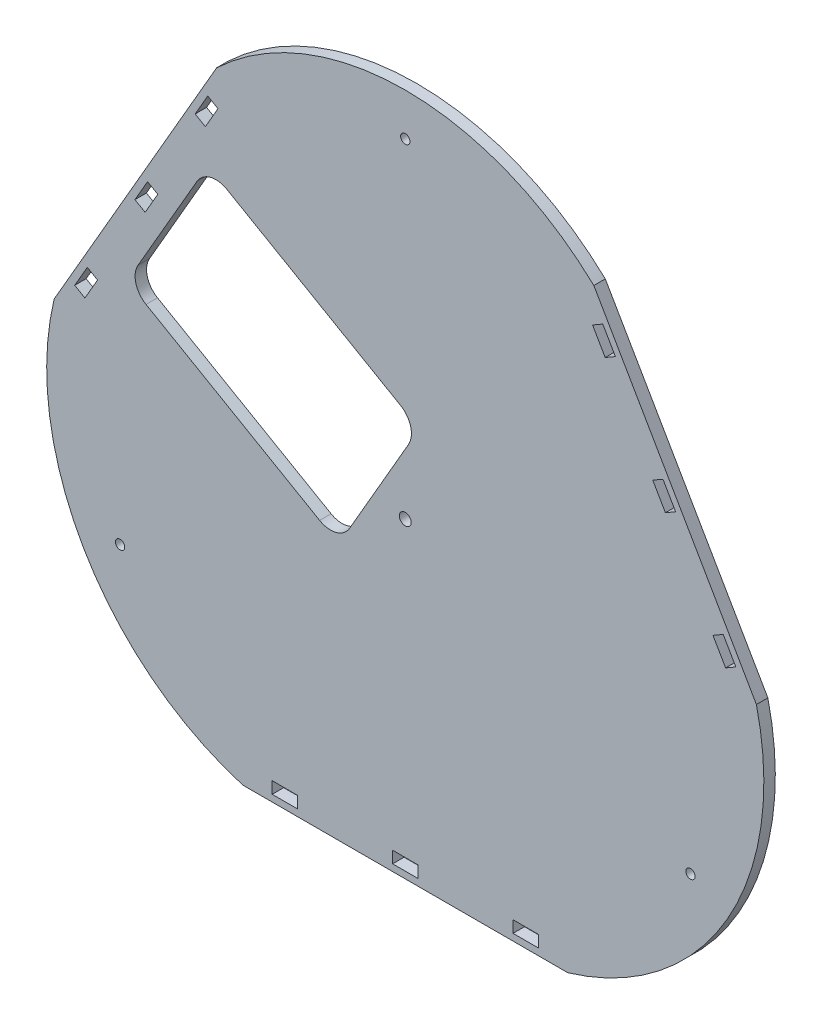
SolidWorks part; units mm, degrees
ref_plane "Front Plane" through (0, 0, 0) normal (0, 0, 1) x (1, 0, 0)
ref_plane "Top Plane" through (0, 0, 0) normal (0, 1, 0) x (1, 0, 0)
ref_plane "Right Plane" through (0, 0, 0) normal (1, 0, 0) x (0, 0, -1)
sketch "Sketch1" plane through (0, 0, 0) normal (0, 0, 1) x (1, 0, 0)
  line L0 (-96.5063, -185) -> (96.5063, -185)
  line L1 (208.4678, 8.9231) -> (111.9616, 176.0769)
  line L2 (-111.9616, 176.0769) -> (-208.4678, 8.9231)
  line L3 (0, 0) -> (-160.2147, 92.5) construction
  line L4 (0, 0) -> (160.2147, 92.5) construction
  line L5 (0, 0) -> (0, -185) construction
  arc A0 (-208.4678, 8.9231) -> (-96.5063, -185) centre (-49.8946, -28.8067) ccw
  arc A1 (96.5063, -185) -> (208.4678, 8.9231) centre (49.8946, -28.8067) ccw
  arc A2 (111.9616, 176.0769) -> (-111.9616, 176.0769) centre (0, 57.6133) ccw
  circle A3 centre (0, 0) radius 3.5
  dimension "D1" = 163
  dimension "D6" = 7
  dimension "D2" = 193.0125
  dimension "D3" = 60
  dimension "D4" = 185
  dimension "D5" = 120
extrude "Boss-Extrude1" add sketch "Sketch1" along normal blind 6.8
sketch "Sketch2" plane through (0, 0, 6.8) normal (0, 0, 1) x (1, 0, 0)
  line L4 (7.5, -174) -> (-7.5, -174)
  line L8 (7.5, -181) -> (7.5, -174)
  line L9 (-7.5, -174) -> (-7.5, -181)
  line L10 (-7.5, -181) -> (7.5, -181)
  line L15 (79, -174) -> (64, -174)
  line L16 (79, -181) -> (79, -174)
  line L17 (64, -174) -> (64, -181)
  line L18 (64, -181) -> (79, -181)
  line L23 (-64, -174) -> (-79, -174)
  line L24 (-64, -181) -> (-64, -174)
  line L25 (-79, -181) -> (-64, -181)
  line L26 (-79, -174) -> (-79, -181)
  line L27 (-96.5063, -185) -> (96.5063, -185) construction
  point P14 (0, -174)
  dimension "D1" = 15
  dimension "D2" = 56.5
  dimension "D3" = 56.5
  dimension "D4" = 7
  dimension "D5" = 4
extrude "Cut-Extrude1" cut sketch "Sketch2" against normal blind 6.8
sketch "Sketch3" plane through (0, 0, 6.8) normal (0, 0, 1) x (1, 0, 0)
  circle A1 centre (0, 195.5) radius 2.75
  dimension "D1" = 5.5
  dimension "D2" = 195.5
extrude "Cut-Extrude2" cut sketch "Sketch3" against normal blind 6.8
pattern_circular "CirPattern1" count 3 over 360 about axis through (0, 0, 0) along (0, 0, 1) of "Cut-Extrude2", "Cut-Extrude1"
sketch "Sketch4" plane through (0, 0, 6.8) normal (0, 0, 1) x (1, 0, 0)
  line L0 (0, 0) -> (-160.2147, 92.5) construction
  line L1 (-111.9616, 176.0769) -> (-208.4678, 8.9231) construction
  line L2 (-117.1621, 123.0692) -> (-165.1621, 39.9308)
  line L3 (-165.1621, 39.9308) -> (-39.5885, -32.5692)
  line L4 (-39.5885, -32.5692) -> (8.4115, 50.5692)
  line L5 (8.4115, 50.5692) -> (-117.1621, 123.0692)
  point P8 (-141.1621, 81.5)
  dimension "D1" = 96
  dimension "D2" = 145
  dimension "D3" = 22
extrude "Cut-Extrude3" cut sketch "Sketch4" against normal blind 6.8
fillet "Fillet1" radius 13 4 edges at (-39.5885, -32.5692, 3.4) (8.4115, 50.5692, 3.4) (-165.1621, 39.9308, 3.4) (-117.1621, 123.0692, 3.4)
